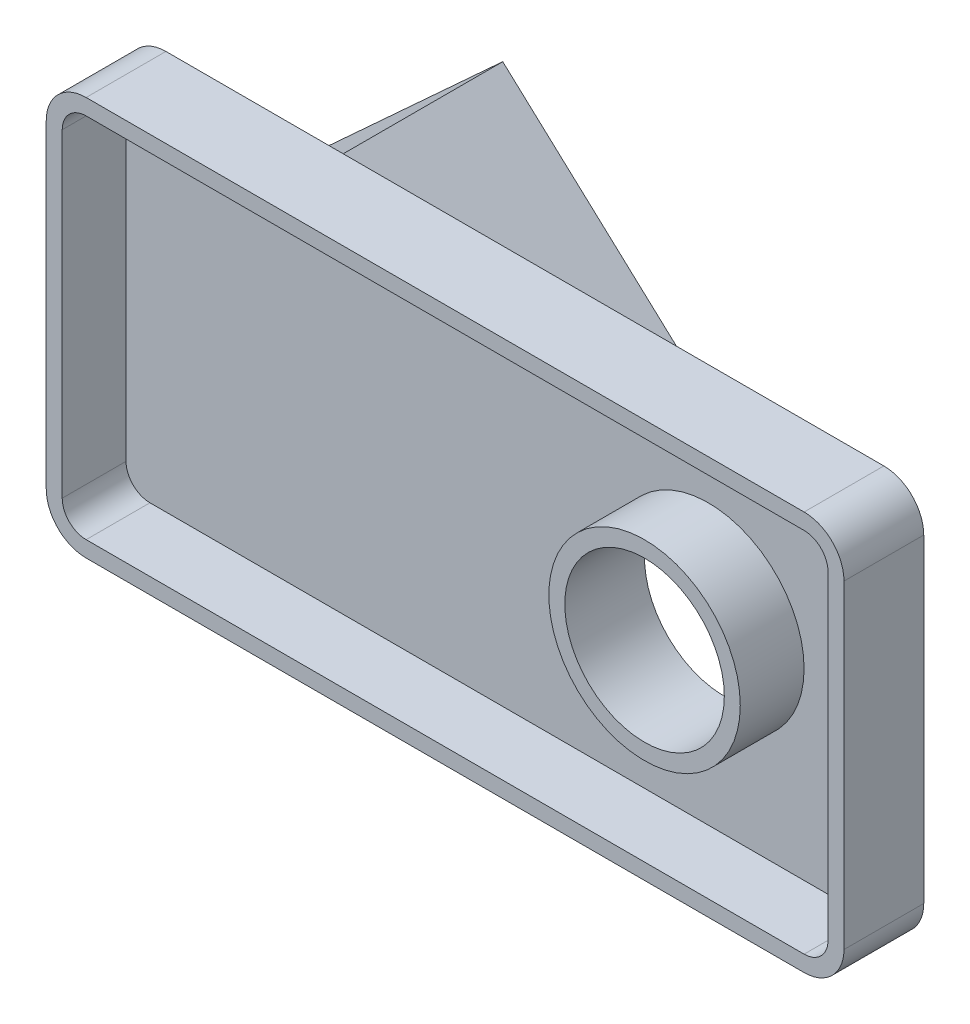
SolidWorks part; units mm, degrees
material "Měď"
ref_plane "Přední rovina" through (0, 0, 0) normal (0, 0, 1) x (1, 0, 0)
ref_plane "Horní rovina" through (0, 0, 0) normal (0, 1, 0) x (1, 0, 0)
ref_plane "Pravá rovina" through (0, 0, 0) normal (1, 0, 0) x (0, 0, -1)
sketch "Skica1" plane through (0, 0, 0) normal (0, 0, 1) x (1, 0, 0)
  line L0 (0, 0) -> (134.5012, 0) construction
  line L1 (100, -50) -> (-100, -50)
  line L2 (100, -50) -> (100, 50)
  line L3 (100, 50) -> (-100, 50)
  line L4 (-100, -50) -> (-100, 50)
  line L5 (100, -50) -> (-100, 50) construction
  line L6 (100, 50) -> (-100, -50) construction
  circle A0 centre (50, 0) radius 20
  point P0 (0, 0)
  dimension "D4" = 40
  dimension "D1" = 200
  dimension "D2" = 100
  dimension "D3" = 50
extrude "Přidat vysunutím1" add sketch "Skica1" along normal blind 20
fillet "Zaoblit1" radius 10 4 edges at (100, -50, 10) (100, 50, 10) (-100, 50, 10) (-100, -50, 10)
shell "Skořepina1" thickness 4
sketch "Skica2" plane through (0, 0, 0) normal (0, 0, -1) x (-1, 0, 0)
  line L0 (45.55, 70.0799) -> (45.55, -50) construction
  line L1 (100, 40) -> (100, -40) construction
  line L2 (0, 0) -> (185.0309, 0) construction
  line L3 (17.5738, -50) -> (63.4789, -50) construction
  line L4 (90, -50) -> (-90, -50) construction
  line L5 (45.55, -50) -> (100, 0)
  line L6 (100, 0) -> (45.55, 50)
  line L7 (-90, 50) -> (90, 50) construction
  line L8 (45.55, -50) -> (-8.9, 0)
  line L9 (-8.9, 0) -> (45.55, 50)
  dimension "D1" = 54.45
  dimension "D2" = 73.9243
  dimension "D3" = 73.9243
extrude "Přidat vysunutím2" add sketch "Skica2" along normal blind 40
